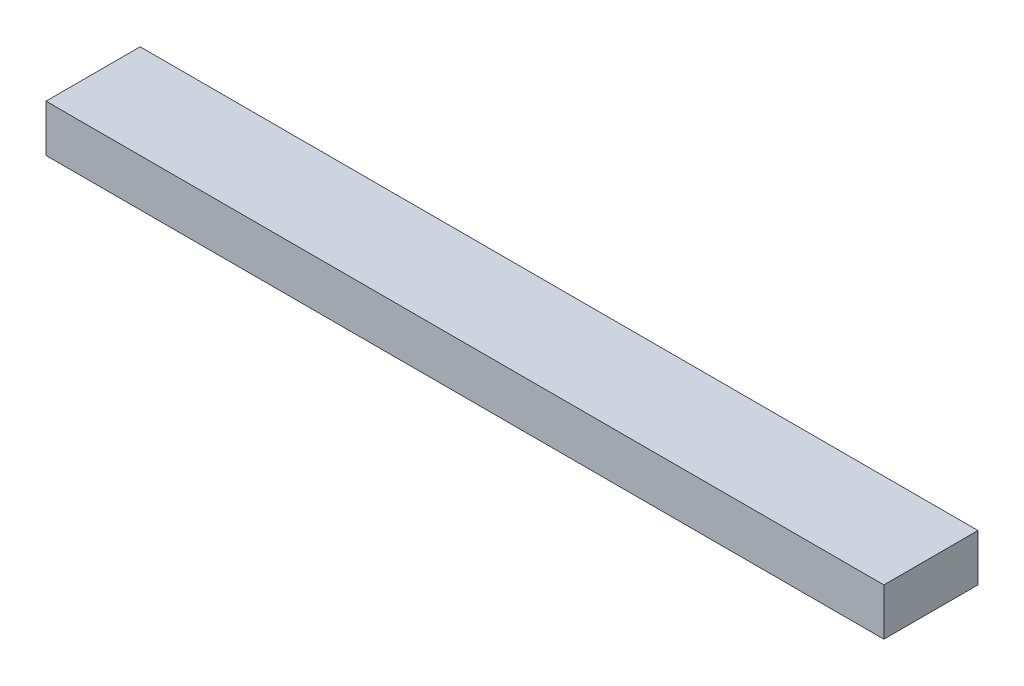
SolidWorks part; units mm, degrees
ref_plane "前视基准面" through (0, 0, 0) normal (0, 0, 1) x (1, 0, 0)
ref_plane "上视基准面" through (0, 0, 0) normal (0, 1, 0) x (1, 0, 0)
ref_plane "右视基准面" through (0, 0, 0) normal (1, 0, 0) x (0, 0, -1)
sketch "草图1" plane through (0, 0, 0) normal (1, 0, 0) x (0, 0, -1)
  line L1 (100, -50) -> (-100, -50)
  line L2 (100, -50) -> (100, 50)
  line L3 (100, 50) -> (-100, 50)
  line L4 (-100, -50) -> (-100, 50)
  line L5 (100, -50) -> (-100, 50) construction
  line L6 (100, 50) -> (-100, -50) construction
  point P0 (0, 0)
extrude "凸台-拉伸1" add sketch "草图1" against normal blind 1780
